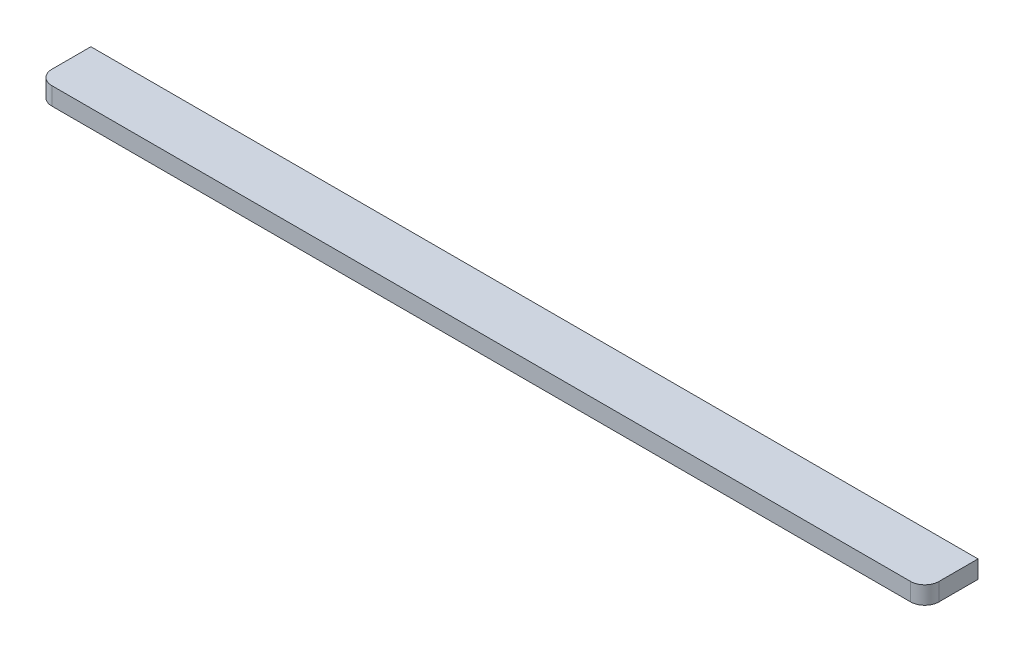
SolidWorks part; units mm, degrees
material "Acrílico (Impacto medio-alto)"
ref_plane "Alzado" through (0, 0, 0) normal (0, 0, 1) x (1, 0, 0)
ref_plane "Planta" through (0, 0, 0) normal (0, 1, 0) x (1, 0, 0)
ref_plane "Vista lateral" through (0, 0, 0) normal (1, 0, 0) x (0, 0, -1)
sketch "Croquis1" plane through (0, 0, 0) normal (0, 1, 0) x (1, 0, 0)
  line L1 (4, 0) -> (246, 0)
  line L2 (0, 4) -> (0, 15)
  line L3 (0, 15) -> (250, 15)
  line L4 (250, 4) -> (250, 15)
  arc A0 (246, 0) -> (250, 4) centre (246, 4) ccw
  arc A1 (4, 0) -> (0, 4) centre (4, 4) cw
  point P7 (250, 0)
  point P10 (0, 0)
  dimension "D3" = 4
  dimension "D4" = 4
  dimension "D1" = 15
  dimension "D2" = 250
extrude "Saliente-Extruir1" add sketch "Croquis1" along normal blind 5
